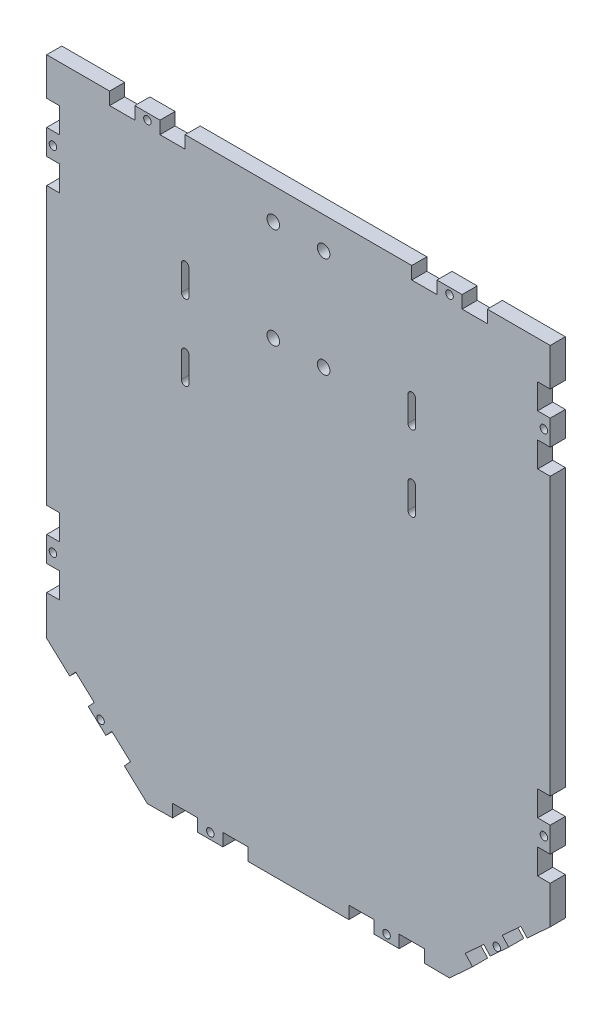
SolidWorks part; units mm, degrees
material "Cedro"
ref_plane "Plano frontal" through (0, 0, 0) normal (0, 0, 1) x (1, 0, 0)
ref_plane "Plano superior" through (0, 0, 0) normal (0, 1, 0) x (1, 0, 0)
ref_plane "Plano direito" through (0, 0, 0) normal (1, 0, 0) x (0, 0, -1)
sketch "Model" plane through (0, 0, 0) normal (0, 0, 1) x (1, 0, 0)
  line L0 (-56.5, -55) -> (-56.5, -45)
  line L1 (-53.5, -45) -> (-53.5, -55)
  line L2 (-53.5, -75) -> (-53.5, -85)
  line L3 (-56.5, -85) -> (-56.5, -75)
  line L4 (-146.5, -85) -> (-146.5, -75)
  line L5 (-143.5, -75) -> (-143.5, -85)
  line L6 (-146.5, -55) -> (-146.5, -45)
  line L7 (-143.5, -45) -> (-143.5, -55)
  line L8 (-5, -175) -> (0, -175)
  line L9 (0, -175) -> (0, -165)
  line L10 (0, -165) -> (-5, -165)
  line L11 (-5, -165) -> (-5, -155)
  line L12 (-5, -155) -> (0, -155)
  line L13 (0, -155) -> (0, -45)
  line L14 (0, -45) -> (-5, -45)
  line L15 (-5, -45) -> (-5, -35)
  line L16 (-5, -35) -> (0, -35)
  line L17 (0, -35) -> (0, -25)
  line L18 (0, -25) -> (-5, -25)
  line L19 (-5, -25) -> (-5, -15)
  line L20 (-5, -15) -> (0, -15)
  line L21 (0, -15) -> (0, 0)
  line L22 (0, 0) -> (-25, 0)
  line L23 (-25, 0) -> (-25, -5)
  line L24 (-25, -5) -> (-35, -5)
  line L25 (-35, -5) -> (-35, 0)
  line L26 (-35, 0) -> (-45, 0)
  line L27 (-45, 0) -> (-45, -5)
  line L28 (-45, -5) -> (-55, -5)
  line L29 (-55, -5) -> (-55, 0)
  line L30 (-55, 0) -> (-145, 0)
  line L31 (-145, 0) -> (-145, -5)
  line L32 (-145, -5) -> (-155, -5)
  line L33 (-155, -5) -> (-155, 0)
  line L34 (-155, 0) -> (-165, 0)
  line L35 (-165, 0) -> (-165, -5)
  line L36 (-165, -5) -> (-175, -5)
  line L37 (-175, -5) -> (-175, 0)
  line L38 (-175, 0) -> (-200, 0)
  line L39 (-200, 0) -> (-200, -15)
  line L40 (-200, -15) -> (-195, -15)
  line L41 (-195, -15) -> (-195, -25)
  line L42 (-195, -25) -> (-200, -25)
  line L43 (-200, -25) -> (-200, -35)
  line L44 (-200, -35) -> (-195, -35)
  line L45 (-195, -35) -> (-195, -45)
  line L46 (-195, -45) -> (-200, -45)
  line L47 (-200, -45) -> (-200, -155)
  line L48 (-200, -155) -> (-195, -155)
  line L49 (-195, -155) -> (-195, -165)
  line L50 (-195, -165) -> (-200, -165)
  line L51 (-200, -165) -> (-200, -175)
  line L52 (-200, -175) -> (-195, -175)
  line L53 (-195, -175) -> (-195, -185)
  line L54 (-195, -185) -> (-200, -185)
  line L55 (-200, -185) -> (-200, -200.7417)
  line L56 (-200, -200.7417) -> (-190.8535, -209.1736)
  line L57 (-190.8535, -209.1736) -> (-188.4813, -206.6003)
  line L58 (-188.4813, -206.6003) -> (-181.1289, -213.3783)
  line L59 (-181.1289, -213.3783) -> (-183.5011, -215.9516)
  line L60 (-183.5011, -215.9516) -> (-176.5015, -222.4042)
  line L61 (-176.5015, -222.4042) -> (-174.097, -219.7959)
  line L62 (-174.097, -219.7959) -> (-166.7416, -226.5766)
  line L63 (-166.7416, -226.5766) -> (-169.1461, -229.1849)
  line L64 (-169.1461, -229.1849) -> (-159.9996, -237.6167)
  line L65 (-159.9996, -237.6167) -> (-150, -237.5328)
  line L66 (-150, -237.5328) -> (-150, -232.5)
  line L67 (-150, -232.5) -> (-140, -232.5)
  line L68 (-140, -232.5) -> (-140, -237.5)
  line L69 (-140, -237.5) -> (-130, -237.5)
  line L70 (-130, -237.5) -> (-130, -232.5)
  line L71 (-130, -232.5) -> (-120, -232.5)
  line L72 (-120, -232.5) -> (-120, -237.5)
  line L73 (-120, -237.5) -> (-80, -237.5)
  line L74 (-80, -237.5) -> (-80, -232.5)
  line L75 (-80, -232.5) -> (-70, -232.5)
  line L76 (-70, -232.5) -> (-70, -237.5)
  line L77 (-70, -237.5) -> (-60, -237.5)
  line L78 (-60, -237.5) -> (-60, -232.5)
  line L79 (-60, -232.5) -> (-50, -232.5)
  line L80 (-50, -232.5) -> (-50, -237.5)
  line L81 (-50, -237.5) -> (-40.0004, -237.5839)
  line L82 (-40.0004, -237.5839) -> (-30.8539, -229.152)
  line L83 (-30.8539, -229.152) -> (-33.7599, -225.9997)
  line L84 (-33.7599, -225.9997) -> (-26.4074, -219.2217)
  line L85 (-26.4074, -219.2217) -> (-23.8521, -221.9936)
  line L86 (-23.8521, -221.9936) -> (-16.4964, -215.2126)
  line L87 (-16.4964, -215.2126) -> (-19.0517, -212.4407)
  line L88 (-19.0517, -212.4407) -> (-11.6992, -205.6627)
  line L89 (-11.6992, -205.6627) -> (-9.1465, -208.4318)
  line L90 (-9.1465, -208.4318) -> (0, -200)
  line L91 (0, -200) -> (0, -185)
  line L92 (0, -185) -> (-5, -185)
  line L93 (-5, -185) -> (-5, -175)
  circle A0 centre (-2.5, -170) radius 1.5
  circle A1 centre (-2.5, -30) radius 1.5
  circle A2 centre (-40, -2.5) radius 1.5
  circle A3 centre (-160, -2.5) radius 1.5
  circle A4 centre (-197.5, -30) radius 1.5
  circle A5 centre (-197.5, -170) radius 1.5
  circle A6 centre (-65, -235) radius 1.5
  circle A7 centre (-135, -235) radius 1.5
  circle A8 centre (-90, -52.5) radius 2.5
  circle A9 centre (-110, -12.5) radius 2.5
  circle A10 centre (-90, -12.5) radius 2.5
  circle A11 centre (-110, -52.5) radius 2.5
  circle A12 centre (-178.6085, -218.0506) radius 1.5
  circle A13 centre (-21.2119, -217.4742) radius 1.5
  arc A14 (-53.5, -45) -> (-56.5, -45) centre (-55, -45) ccw
  arc A15 (-56.5, -55) -> (-53.5, -55) centre (-55, -55) ccw
  arc A16 (-53.5, -75) -> (-56.5, -75) centre (-55, -75) ccw
  arc A17 (-56.5, -85) -> (-53.5, -85) centre (-55, -85) ccw
  arc A18 (-146.5, -85) -> (-143.5, -85) centre (-145, -85) ccw
  arc A19 (-143.5, -75) -> (-146.5, -75) centre (-145, -75) ccw
  arc A20 (-143.5, -45) -> (-146.5, -45) centre (-145, -45) ccw
  arc A21 (-146.5, -55) -> (-143.5, -55) centre (-145, -55) ccw
  dimension "D1" = 12.44
  dimension "D3" = 10
  dimension "D5" = 9.52
  dimension "D8" = 90
  dimension "D9" = 10
  dimension "D11" = 136.848
  dimension "D12" = 90
  dimension "D13" = 90
  dimension "D14" = 90
  dimension "D15" = 12.44
  dimension "D16" = 4.5
  dimension "D17" = 10
  dimension "D18" = 136.848
  dimension "D19" = 90
  dimension "D20" = 10
  dimension "D21" = 90
  dimension "D22" = 90
  dimension "D23" = 90
  dimension "D24" = 90
  dimension "D25" = 90
  dimension "D26" = 132.672
  dimension "D27" = 132.672
  dimension "D28" = 90
  dimension "D29" = 90
  dimension "D30" = 10
  dimension "D31" = 12.44
  dimension "D32" = 12.44
  dimension "D33" = 10.0045
  dimension "D34" = 5
  dimension "D35" = 3.7662
  dimension "D36" = 3.77
  dimension "D37" = 3.77
extrude "Ressalto-extrusão1" add sketch "Model" along normal blind 6
